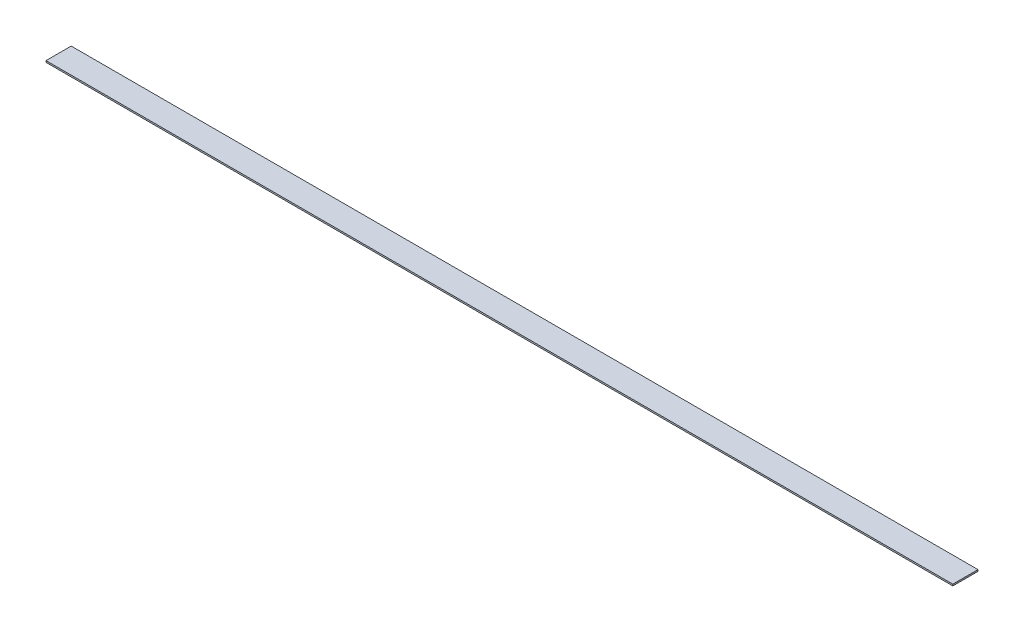
SolidWorks part; units mm, degrees
ref_plane "Front Plane" through (0, 0, 0) normal (0, 0, 1) x (1, 0, 0)
ref_plane "Top Plane" through (0, 0, 0) normal (0, 1, 0) x (1, 0, 0)
ref_plane "Right Plane" through (0, 0, 0) normal (1, 0, 0) x (0, 0, -1)
sketch "Sketch1" plane through (0, 0, 0) normal (0, 1, 0) x (1, 0, 0)
  line L1 (0, 0) -> (914.4, 0)
  line L2 (0, 0) -> (0, 25.4)
  line L3 (0, 25.4) -> (914.4, 25.4)
  line L4 (914.4, 0) -> (914.4, 25.4)
  dimension "D1" = 25.4
  dimension "D2" = 914.4
extrude "Boss-Extrude1" add sketch "Sketch1" along normal blind 1.5875
